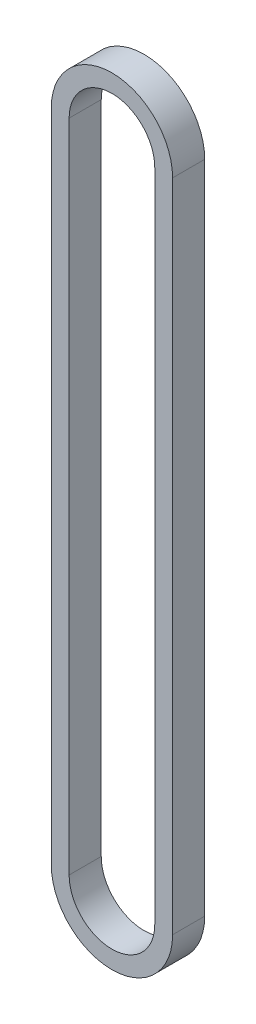
SolidWorks part; units mm, degrees
material "Найлон 6/10"
ref_plane "Спереди" through (0, 0, 0) normal (0, 0, 1) x (1, 0, 0)
ref_plane "Сверху" through (0, 0, 0) normal (0, 1, 0) x (1, 0, 0)
ref_plane "Справа" through (0, 0, 0) normal (1, 0, 0) x (0, 0, -1)
sketch "Эскиз1" plane through (0, 0, 0) normal (0, 0, 1) x (1, 0, 0)
  line L0 (0, -45.925) -> (0, 45.925) construction
  line L1 (-8.5, -45.925) -> (-8.5, 45.925)
  line L2 (8.5, -45.925) -> (8.5, 45.925)
  line L3 (0, -45.925) -> (0, 45.925) construction
  line L4 (-6, -45.925) -> (-6, 45.925)
  line L5 (6, -45.925) -> (6, 45.925)
  arc A0 (-8.5, -45.925) -> (8.5, -45.925) centre (0, -45.925) ccw
  arc A1 (8.5, 45.925) -> (-8.5, 45.925) centre (0, 45.925) ccw
  arc A2 (-6, -45.925) -> (6, -45.925) centre (0, -45.925) ccw
  arc A3 (6, 45.925) -> (-6, 45.925) centre (0, 45.925) ccw
  point P3 (0, 0)
  point P10 (0, 0)
  dimension "D1" = 91.85
  dimension "D2" = 17
  dimension "D3" = 2.5
extrude "Бобышка-Вытянуть1" add sketch "Эскиз1" along normal blind 4.5
